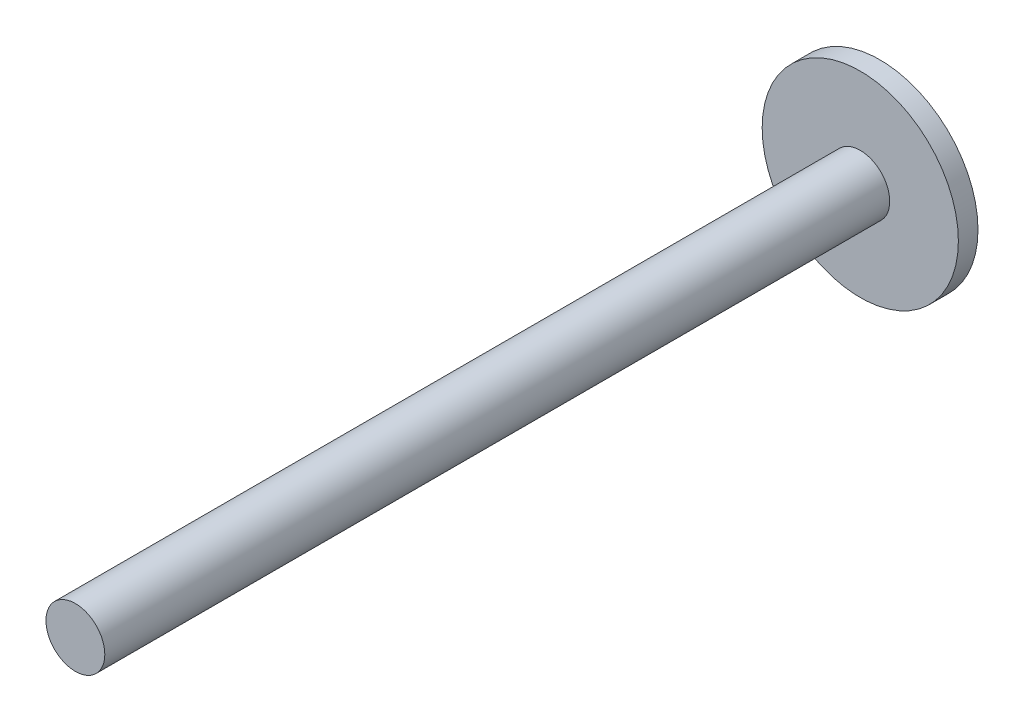
SolidWorks part; units mm, degrees
ref_plane "Front Plane" through (0, 0, 0) normal (0, 0, 1) x (1, 0, 0)
ref_plane "Top Plane" through (0, 0, 0) normal (0, 1, 0) x (1, 0, 0)
ref_plane "Right Plane" through (0, 0, 0) normal (1, 0, 0) x (0, 0, -1)
sketch "Sketch1" plane through (0, 0, 0) normal (0, 0, 1) x (1, 0, 0)
  circle A0 centre (0, 0) radius 450
  dimension "D1" = 900
extrude "Boss-Extrude1" add sketch "Sketch1" along normal blind 12000
sketch "Sketch2" plane through (0, 0, 0) normal (0, 0, -1) x (-1, 0, 0)
  circle A0 centre (0, 0) radius 1500
  dimension "D1" = 3000
extrude "Boss-Extrude2" add sketch "Sketch2" along normal blind 300
